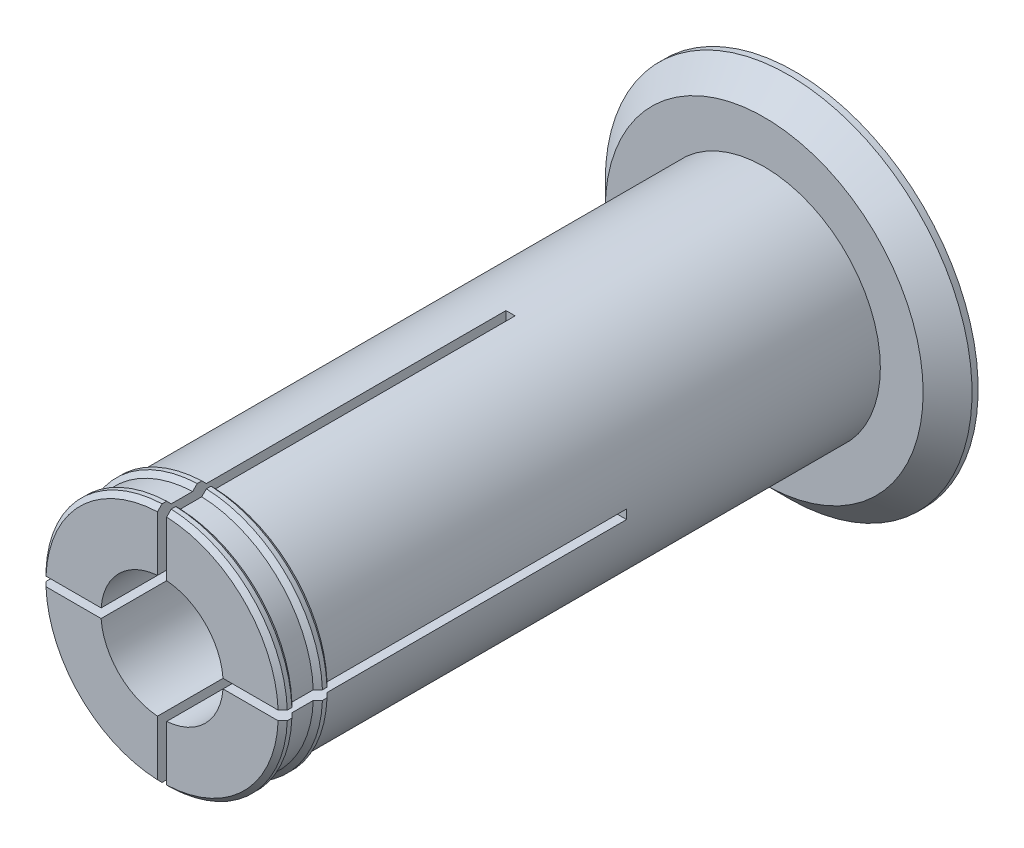
SolidWorks part; units mm, degrees
ref_plane "Front" through (0, 0, 0) normal (0, 0, 1) x (1, 0, 0)
ref_plane "Top" through (0, 0, 0) normal (0, 1, 0) x (1, 0, 0)
ref_plane "Right" through (0, 0, 0) normal (1, 0, 0) x (0, 0, -1)
sketch "Axle base sketch" plane through (0, 0, 0) normal (0, 0, 1) x (1, 0, 0)
  circle A0 centre (0, 0) radius 19
  dimension "D1" = 38
extrude "Axle" add sketch "Axle base sketch" along normal blind 98.5
sketch "Guard base" plane through (0, 0, 0) normal (0, 0, -1) x (-1, 0, 0)
  circle A0 centre (0, 0) radius 30
  dimension "D1" = 60
extrude "Guard" add sketch "Guard base" along normal blind 5
sketch "Inner axle hole base" plane through (0, 0, 98.5) normal (0, 0, 1) x (1, 0, 0)
  circle A0 centre (0, 0) radius 10
  dimension "D1" = 20
extrude "Inner axle hole" cut sketch "Inner axle hole base" against normal through all
sketch "Mate ring base" plane through (0, 0, 0) normal (0, 1, 0) x (1, 0, 0)
  line L0 (19, -98.5) -> (19.75, -97.75)
  line L1 (19.75, -97.75) -> (19.75, -97)
  line L2 (19.75, -97) -> (19, -96.25)
  line L3 (19.75, -97.75) -> (19.75, -98.5) construction
  line L4 (19.75, -98.5) -> (19, -98.5) construction
  line L5 (19, -96.25) -> (19, -98.5)
  line L6 (19, -98.5) -> (19, 0) construction
  line L8 (19, -92.75) -> (19.75, -92)
  line L9 (19.75, -92) -> (19.75, -91.25)
  line L10 (19.75, -91.25) -> (19, -90.5)
  line L11 (19, -90.5) -> (19, -92.75)
  dimension "D1" = 0.75
  dimension "D2" = 0.75
  dimension "D3" = 5
  dimension "D4" = 0.75
ref_axis "Center Z" through (0, 0, 0) along (0, 0, -1)
revolve "Mate rings" add sketch "Mate ring base" angle 360 about axis through (0, 0, 0) along (0, 0, -1)
sketch "Bend room base" plane through (0, 0, 98.5) normal (0, 0, 1) x (1, 0, 0)
  line L0 (0.75, -25) -> (0.75, 25)
  line L1 (0.75, 25) -> (-0.75, 25)
  line L2 (-0.75, 25) -> (-0.75, -25)
  line L3 (-0.75, -25) -> (0.75, -25)
  dimension "D1" = 0.75
  dimension "D2" = 0.75
  dimension "D3" = 25
  dimension "D4" = 25
extrude "Bend room 1" cut sketch "Bend room base" against normal blind 57
pattern_circular "Bend room 2" count 2 every 90 about axis through (0, 0, 0) along (0, 0, -1) of "Bend room 1"
chamfer "Easy removal chamfer" distance 4 angle 45 1 edges at (-30, 0, 0)
equation "\"32_92_spool_inner_diameter\"=32"
equation "\"D1@Axle base sketch\"=\"39_92_spool_inner_diameter\"- \"spool_inner_diameter_room\""
equation "\"spool_inner_diameter_room\"=1"
equation "\"32_92_spool_thickness\"=92"
equation "\"D1@Axle\"=\"39_92_spool_thickness\"+\"guard_thickness\"+\"removal_room\"*2"
equation "\"32_92_guard_diameter\"=50"
equation "\"D1@Guard base\"=\"39_92_guard_diameter\""
equation "\"guard_thickness\"=5"
equation "\"D1@Guard\"=\"guard_thickness\""
equation "\"large_inner_axle_diameter\"=20"
equation "\"D1@Inner axle hole base\"=\"large_inner_axle_diameter\""
equation "\"mate_room\"= 0.25"
equation "\"removal_room\"= 0.75"
equation "\"small_inner_axle_diameter\"=17"
equation "\"53_55_spool_inner_diameter\"=53"
equation "\"53_55_spool_thickness\"=55"
equation "\"53_55_guard_diameter\"=75"
equation "\"53_55_coupling_tooth_height\"=27"
equation "\"53_55_coupling_tooth_thickness_total\"=8"
equation "\"53_55_coupling_tooth_protrusion\"=1.5"
equation "\"53_55_coupling_tooth_head_height\"=7.5"
equation "\"53_55_coupling_tooth_depth\"=10"
equation "\"53_55_coupling_tooth_base_thickness\"=9.5"
equation "\"D1@Mate ring base\"=\"removal_room\""
equation "\"D2@Mate ring base\"=\"removal_room\""
equation "\"D3@Mate ring base\"=\"guard_thickness\""
equation "\"D4@Mate ring base\"=\"removal_room\""
equation "\"D1@Bend room base\" = \"removal_room\""
equation "\"D2@Bend room base\"=\"removal_room\""
equation "\"D3@Bend room base\"=\"32_92_guard_diameter\"/2"
equation "\"D4@Bend room base\"=\"32_92_guard_diameter\"/2"
equation "\"bend_room_length_multiplier\"=3"
equation "\"D1@Bend room 1\"=\"bend_room_length_multiplier\"*(\"39_92_spool_inner_diameter\"-\"large_inner_axle_diameter\")"
equation "\"D1@Easy removal chamfer\"=\"guard_thickness\"-1"
equation "\"32_92_extra_spool_thickness\"=-5"
equation "\"39_92_spool_inner_diameter\"=39"
equation "\"39_92_spool_thickness\"=92"
equation "\"39_92_guard_diameter\"=60"
